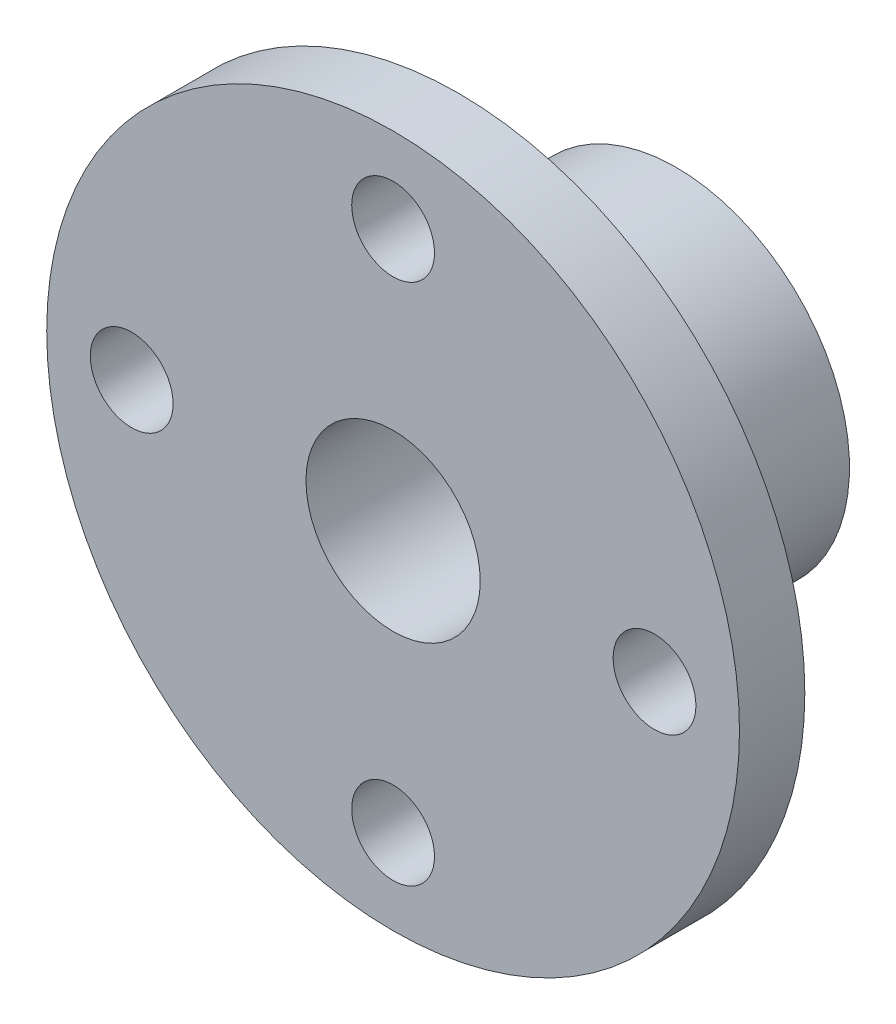
SolidWorks part; units mm, degrees
ref_plane "Front Plane" through (0, 0, 0) normal (0, 0, 1) x (1, 0, 0)
ref_plane "Top Plane" through (0, 0, 0) normal (0, 1, 0) x (1, 0, 0)
ref_plane "Right Plane" through (0, 0, 0) normal (1, 0, 0) x (0, 0, -1)
sketch "Sketch1" plane through (0, 0, 0) normal (0, 0, 1) x (1, 0, 0)
  circle A0 centre (0, 0) radius 15.9
  dimension "D1" = 31.8
extrude "Boss-Extrude1" add sketch "Sketch1" along normal blind 3
sketch "Sketch2" plane through (0, 0, 0) normal (0, 0, -1) x (-1, 0, 0)
  circle A0 centre (0, 0) radius 7.95
  dimension "D1" = 15.9
extrude "Boss-Extrude2" add sketch "Sketch2" along normal blind 10
sketch "Sketch3" plane through (0, 0, -10) normal (0, 0, -1) x (-1, 0, 0)
  circle A0 centre (0, 0) radius 4
  dimension "D1" = 8
extrude "Cut-Extrude1" cut sketch "Sketch3" against normal blind 20
sketch "Sketch4" plane through (0, 0, 0) normal (0, 0, -1) x (-1, 0, 0)
  line L0 (0, 19.6163) -> (0, -18.1626) construction
  line L1 (-22.4893, 0) -> (21.4861, 0) construction
  circle A0 centre (0, 12) radius 1.9
  circle A1 centre (-12, 0) radius 1.9
  circle A2 centre (12, 0) radius 1.9
  circle A3 centre (0, -12) radius 1.9
  dimension "D1" = 3.8
  dimension "D3" = 3.8
  dimension "D2" = 12
  dimension "D4" = 12
extrude "Cut-Extrude2" cut sketch "Sketch4" against normal blind 20
